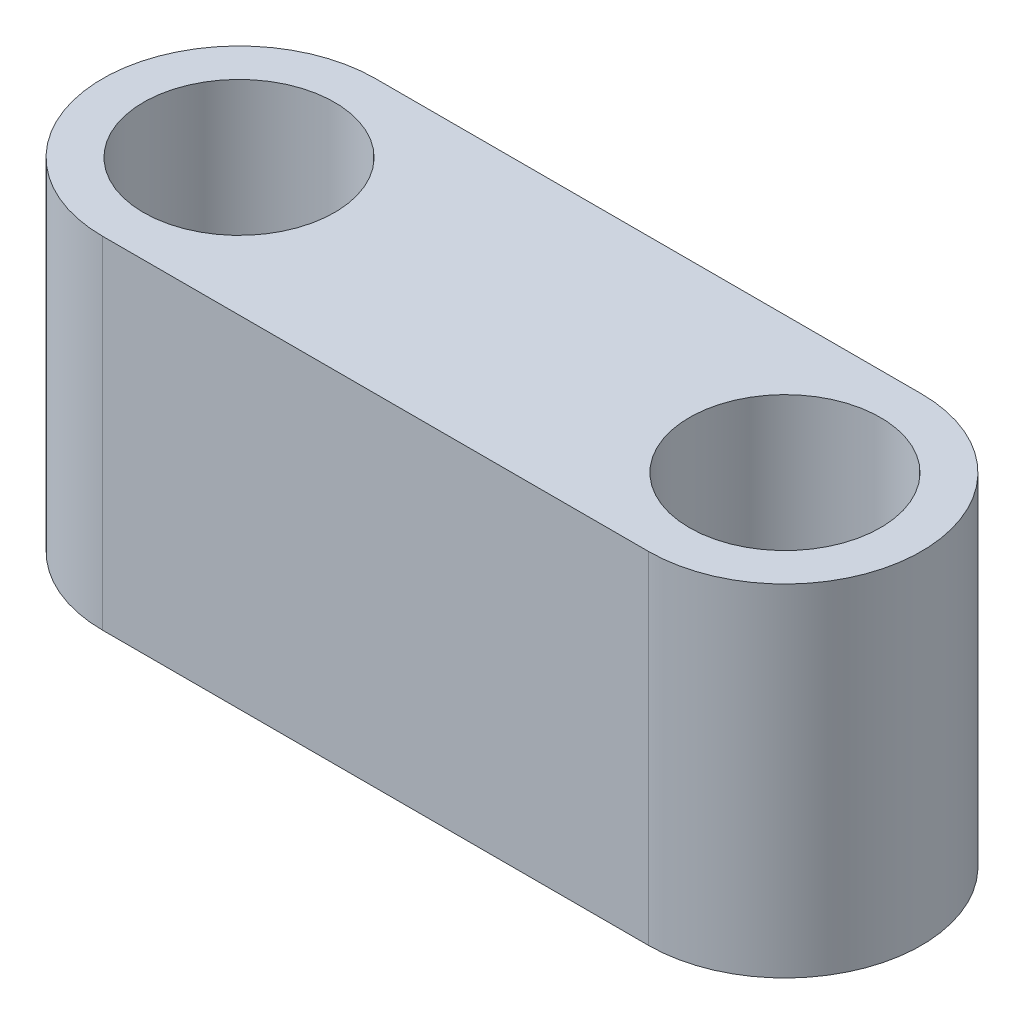
SolidWorks part; units mm, degrees
ref_plane "Front Plane" through (0, 0, 0) normal (0, 0, 1) x (1, 0, 0)
ref_plane "Top Plane" through (0, 0, 0) normal (0, 1, 0) x (1, 0, 0)
ref_plane "Right Plane" through (0, 0, 0) normal (1, 0, 0) x (0, 0, -1)
sketch "Sketch1" plane through (0, 0, 0) normal (0, 1, 0) x (1, 0, 0)
  line L0 (-40, 0) -> (40, 0) construction
  line L1 (-40, 20) -> (40, 20)
  line L2 (-40, -20) -> (40, -20)
  circle A0 centre (40, 0) radius 14
  circle A1 centre (-40, 0) radius 14
  arc A2 (-40, 20) -> (-40, -20) centre (-40, 0) ccw
  arc A3 (40, -20) -> (40, 20) centre (40, 0) ccw
  dimension "D2" = 28
  dimension "D3" = 20
  dimension "D1" = 80
extrude "Boss-Extrude1" add sketch "Sketch1" along normal blind 50
